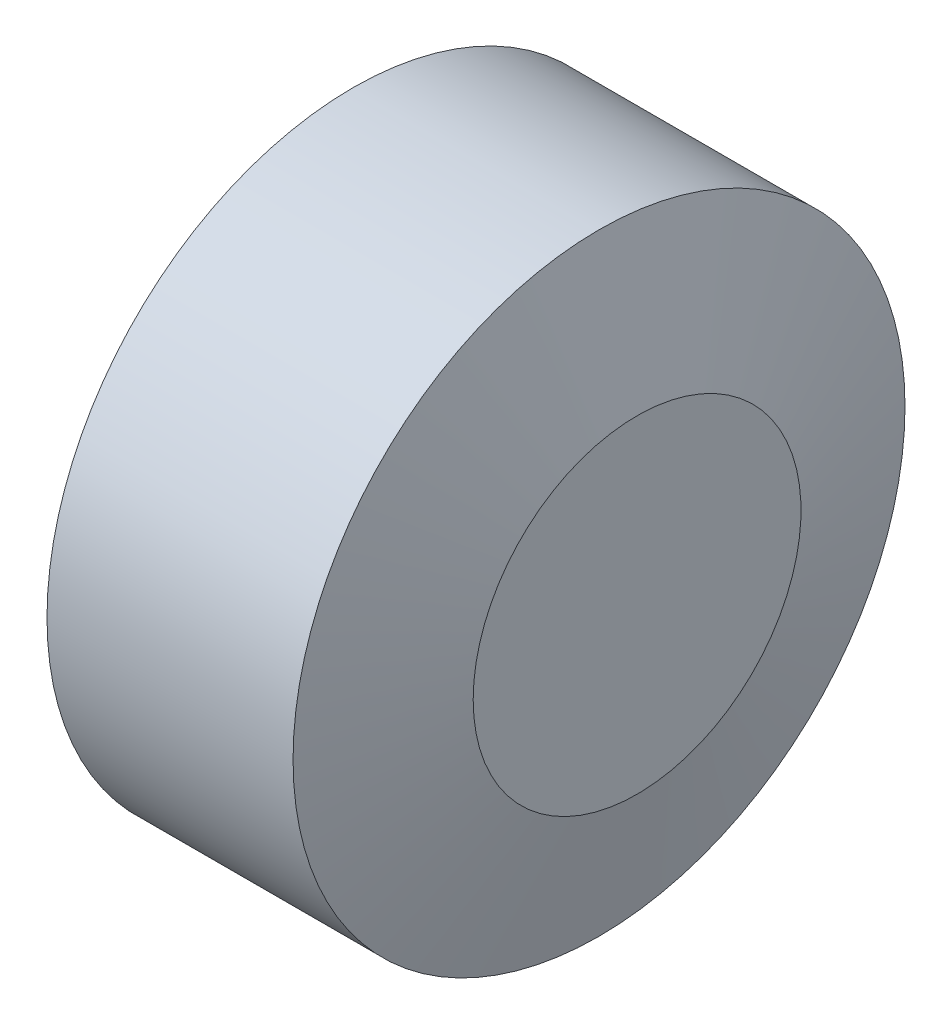
SolidWorks part; units mm, degrees
ref_plane "Ebene vorne" through (0, 0, 0) normal (0, 0, 1) x (1, 0, 0)
ref_plane "Ebene oben" through (0, 0, 0) normal (0, 1, 0) x (1, 0, 0)
ref_plane "Ebene rechts" through (0, 0, 0) normal (1, 0, 0) x (0, 0, -1)
sketch "Skizze1" plane through (0, 0, 0) normal (0, 0, 1) x (1, 0, 0)
  line L0 (0, 0) -> (56.0834, 0) construction
  line L1 (0, 0) -> (0, -14)
  line L2 (0, -14) -> (11.2583, -14)
  line L3 (11.2583, -14) -> (13, -7.5)
  line L4 (13, -7.5) -> (13, 0)
  line L5 (0, 0) -> (13, 0)
  dimension "D1" = 28
  dimension "D2" = 15
  dimension "D3" = 13
  dimension "D4" = 15
revolve "Rotation1" add sketch "Skizze1" angle 360 about L0
sketch "Skizze13" plane through (13, 0, 0) normal (1, 0, 0) x (0, 0, -1)
  line L0 (11.2845, 1.5799) -> (11.3741, 0.6083)
  line L1 (11.3741, 0.6083) -> (11.2845, 1.5799)
  line L2 (12.3428, 1.2588) -> (9.452, 0.9909)
  line L4 (9.5613, 3.6387) -> (9.5927, 2.9574)
  line L5 (8.5478, 3.7436) -> (8.6967, 3.8751)
  line L7 (8.7106, 5.0765) -> (7.4768, 6.7494)
  line L9 (6.869, 10.1322) -> (4.9357, 7.2875)
  line L10 (4.9357, 7.2875) -> (6.869, 10.1322)
  line L11 (5.8093, 10.8519) -> (7.9286, 9.4117)
  line L12 (7.9286, 9.4117) -> (5.8093, 10.8519)
  circle A1 centre (0, 0) radius 8.9821 construction
  spline S0 degree 3 poles (9.452, 0.9909) (9.4078, 0.9865) (9.3416, 0.9742) (9.2592, 0.9408) (9.2001, 0.9101) (9.1449, 0.8728) (9.0789, 0.8122) (9.0356, 0.7605) (9.0135, 0.7209) knots 0 0 0 0 0.250138 0.374097 0.498215 0.623467 0.746733 1 1 1 1
  spline S1 degree 3 poles (9.0135, 0.7209) (8.9889, 0.684) (8.961, 0.6237) (8.9352, 0.539) (8.9234, 0.4736) (8.9192, 0.4069) (8.9238, 0.3172) (8.9394, 0.2511) (8.954, 0.2083) knots 0 0 0 0 0.248261 0.371336 0.496457 0.621138 0.745744 1 1 1 1
  spline S2 degree 3 poles (10.5482, 2.721) (10.6028, 2.7556) (10.7013, 2.8473) (10.759, 2.9687) (10.779, 3.0329) knots 0 0 0 0 0.489493 1 1 1 1
  spline S3 degree 3 poles (10.779, 3.0329) (10.7979, 3.0978) (10.8228, 3.2352) (10.8159, 3.3745) (10.807, 3.4449) knots 0 0 0 0 0.487714 1 1 1 1
  spline S4 degree 3 poles (10.807, 3.4449) (10.7969, 3.5156) (10.762, 3.6557) (10.7041, 3.7878) (10.6692, 3.8513) knots 0 0 0 0 0.49623 1 1 1 1
  spline S5 degree 3 poles (10.6692, 3.8513) (10.6339, 3.9127) (10.5568, 4.0246) (10.4571, 4.117) (10.4041, 4.1534) knots 0 0 0 0 0.52472 1 1 1 1
  spline S6 degree 3 poles (10.4041, 4.1534) (10.3566, 4.1885) (10.2561, 4.2492) (10.1407, 4.2733) (10.0837, 4.2731) knots 0 0 0 0 0.510177 1 1 1 1
  spline S7 degree 3 poles (10.0837, 4.2731) (10.0271, 4.2755) (9.9056, 4.2516) (9.8009, 4.1862) (9.7501, 4.1458) knots 0 0 0 0 0.464078 1 1 1 1
  spline S8 degree 3 poles (9.7501, 4.1458) (9.7231, 4.1204) (9.6846, 4.077) (9.6474, 4.0071) (9.621, 3.9472) (9.5997, 3.8798) (9.5757, 3.7769) (9.5655, 3.6952) (9.5613, 3.6387) knots 0 0 0 0 0.201067 0.31074 0.427827 0.555243 0.692797 1 1 1 1
  spline S9 degree 3 poles (9.5927, 2.9574) (9.5964, 2.8899) (9.5966, 2.7631) (9.5665, 2.6398) (9.5459, 2.5853) knots 0 0 0 0 0.537618 1 1 1 1
  spline S10 degree 3 poles (9.5459, 2.5853) (9.5271, 2.5357) (9.4771, 2.4431) (9.4066, 2.365) (9.3675, 2.3314) knots 0 0 0 0 0.507486 1 1 1 1
  spline S11 degree 3 poles (9.3675, 2.3314) (9.3271, 2.2998) (9.2348, 2.2488) (9.13, 2.2362) (9.0779, 2.2384) knots 0 0 0 0 0.495838 1 1 1 1
  spline S12 degree 3 poles (9.0779, 2.2384) (9.022, 2.2405) (8.9062, 2.2649) (8.8027, 2.3221) (8.7527, 2.3573) knots 0 0 0 0 0.477202 1 1 1 1
  spline S13 degree 3 poles (8.7527, 2.3573) (8.6992, 2.3921) (8.6, 2.4853) (8.5226, 2.597) (8.4876, 2.6594) knots 0 0 0 0 0.470377 1 1 1 1
  spline S14 degree 3 poles (8.4876, 2.6594) (8.4508, 2.7209) (8.3921, 2.8532) (8.3592, 2.994) (8.3498, 3.0658) knots 0 0 0 0 0.497265 1 1 1 1
  spline S15 degree 3 poles (8.3498, 3.0658) (8.3394, 3.1345) (8.3344, 3.2712) (8.3595, 3.4057) (8.3813, 3.4687) knots 0 0 0 0 0.510753 1 1 1 1
  spline S16 degree 3 poles (8.3813, 3.4687) (8.3981, 3.5244) (8.4412, 3.6249) (8.5085, 3.7115) (8.5478, 3.7436) knots 0 0 0 0 0.536048 1 1 1 1
  spline S17 degree 3 poles (8.0098, 4.8366) (7.9364, 4.8344) (7.7891, 4.8419) (7.6461, 4.8784) (7.5768, 4.9023) knots 0 0 0 0 0.500142 1 1 1 1
  spline S18 degree 3 poles (7.5768, 4.9023) (7.5316, 4.9195) (7.4648, 4.947) (7.3821, 4.9952) (7.3241, 5.0352) (7.2688, 5.0785) (7.2182, 5.1273) (7.1693, 5.1789) (7.1251, 5.2354) (7.0847, 5.2946) (7.0484, 5.3557) (7.0187, 5.4194) (6.9936, 5.4847) (6.9721, 5.5513) (6.9514, 5.6439) (6.9451, 5.7154) (6.9424, 5.7633) knots 0 0 0 0 0.127666 0.190265 0.252235 0.31356 0.375383 0.437654 0.501191 0.564524 0.626591 0.688537 0.749914 0.811229 0.873046 1 1 1 1
  spline S19 degree 3 poles (6.9424, 5.7633) (6.9408, 5.866) (6.9568, 6.0199) (7.0151, 6.2171) (7.0777, 6.3586) (7.1555, 6.4926) (7.2798, 6.6571) (7.3933, 6.7627) (7.4761, 6.8237) knots 0 0 0 0 0.249815 0.373527 0.49931 0.625449 0.749841 1 1 1 1
  spline S20 degree 3 poles (7.4761, 6.8237) (7.5584, 6.8856) (7.6933, 6.9619) (7.8871, 7.0318) (8.0379, 7.0664) (8.1916, 7.0843) (8.3976, 7.0824) (8.5498, 7.0522) (8.6476, 7.0202) knots 0 0 0 0 0.250179 0.374318 0.500057 0.625629 0.749837 1 1 1 1
  spline S21 degree 3 poles (8.6476, 7.0202) (8.693, 7.0042) (8.7589, 6.976) (8.841, 6.9286) (8.8992, 6.8898) (8.9532, 6.8455) (9.0054, 6.7986) (9.0525, 6.7455) (9.0976, 6.6899) (9.1379, 6.6306) (9.1734, 6.5691) (9.2047, 6.506) (9.2296, 6.4402) (9.251, 6.3729) (9.271, 6.2792) (9.2809, 6.2077) (9.282, 6.1592) knots 0 0 0 0 0.12689 0.188652 0.250278 0.311125 0.372982 0.435293 0.498351 0.561688 0.62429 0.685951 0.747331 0.809824 0.872245 1 1 1 1
  spline S22 degree 3 poles (9.282, 6.1592) (9.2836, 6.0531) (9.2682, 5.8934) (9.206, 5.6896) (9.1401, 5.5436) (9.0572, 5.4067) (8.924, 5.239) (8.8001, 5.1354) (8.7106, 5.0765) knots 0 0 0 0 0.249225 0.373386 0.498834 0.624353 0.74823 1 1 1 1
sketch "Skizze14" plane through (13, 0, 0) normal (1, 0, 0) x (0, 0, -1)
  line L1 (8.7106, 5.0765) -> (7.4768, 6.7494) construction
  line L2 (8.7106, 5.0765) -> (7.4768, 6.7494)
  spline S0 degree 3 poles (-1504.7271, -1303.0515) (34.3407, 79.4947) (-4.2637, -73.8144) (4.661, 87.6769) (1231.772, -1576.2357) knots -50.963163 -50.963163 -50.963163 -50.963163 0.500142 53.15614 53.15614 53.15614 53.15614 only from (8.0098, 4.8366) to (7.5768, 4.9023) construction
  spline S1 degree 3 poles (-1103.2655, -1658.161) (30.3504, 31.0888) (11.0666, 2.8493) (7.3821, 4.9952) (7.3241, 5.0352) (7.2688, 5.0785) (7.2182, 5.1273) (7.1693, 5.1789) (7.1251, 5.2354) (7.0847, 5.2946) (7.0484, 5.3557) (7.0187, 5.4194) (6.9936, 5.4847) (6.9721, 5.5513) (5.9893, 9.9536) (41.2588, 20.4289) (-1904.0188, -583.9593) knots -10.987318 -10.987318 -10.987318 -10.987318 0.127666 0.190265 0.252235 0.31356 0.375383 0.437654 0.501191 0.564524 0.626591 0.688537 0.749914 0.811229 0.873046 12.638524 12.638524 12.638524 12.638524 only from (7.5768, 4.9023) to (6.9424, 5.7633) construction
  spline S2 degree 3 poles (290.3759, 1984.1174) (99.2879, -33.5022) (4.4077, -2.6079) (7.0151, 6.2171) (7.0777, 6.3586) (7.1555, 6.4926) (12.8733, 14.0641) (95.4639, -44.1594) (-1427.223, -1384.4174) knots -21.837368 -21.837368 -21.837368 -21.837368 0.249815 0.373527 0.49931 0.625449 0.749841 23.536745 23.536745 23.536745 23.536745 only from (6.9424, 5.7633) to (7.4761, 6.8237) construction
  spline S3 degree 3 poles (1982.0417, -304.7734) (23.8517, -74.9215) (-0.3269, 4.0696) (7.8871, 7.0318) (8.0379, 7.0664) (8.1916, 7.0843) (17.28, 7.0015) (19.0596, -91.9283) (-1935.5645, 470.107) knots -20.692282 -20.692282 -20.692282 -20.692282 0.250179 0.374318 0.500057 0.625629 0.749837 22.549034 22.549034 22.549034 22.549034 only from (7.4761, 6.8237) to (8.6476, 7.0202) construction
  spline S4 degree 3 poles (1813.2868, 868.7619) (-33.1273, -45.2984) (3.3889, 10.0808) (8.841, 6.9286) (8.8992, 6.8898) (8.9532, 6.8455) (9.0054, 6.7986) (9.0525, 6.7455) (9.0976, 6.6899) (9.1379, 6.6306) (9.1734, 6.5691) (9.2047, 6.506) (9.2296, 6.4402) (9.251, 6.3729) (10.1299, 2.2648) (-6.5263, -5.0538) (-1990.0024, -42.644) knots -16.36419 -16.36419 -16.36419 -16.36419 0.12689 0.188652 0.250278 0.311125 0.372982 0.435293 0.498351 0.561688 0.62429 0.685951 0.747331 0.809824 0.872245 11.827501 11.827501 11.827501 11.827501 only from (8.6476, 7.0202) to (9.282, 6.1592) construction
  spline S5 degree 3 poles (858.7258, -1803.8846) (-75.3502, 42.7074) (11.7151, 13.9046) (9.206, 5.6896) (9.1401, 5.5436) (9.0572, 5.4067) (3.6749, -1.3688) (-70.8363, 55.1198) (1947.1145, 494.5404) knots -19.608757 -19.608757 -19.608757 -19.608757 0.249225 0.373386 0.498834 0.624353 0.74823 20.755578 20.755578 20.755578 20.755578 only from (9.282, 6.1592) to (8.7106, 5.0765) construction
  spline S6 degree 3 poles (8.0098, 4.8366) (7.9364, 4.8344) (7.7891, 4.8419) (7.6461, 4.8784) (7.5768, 4.9023) knots 0 0 0 0 0.500142 1 1 1 1
  spline S7 degree 3 poles (7.5768, 4.9023) (7.5316, 4.9195) (7.4648, 4.947) (7.3821, 4.9952) (7.3241, 5.0352) (7.2688, 5.0785) (7.2182, 5.1273) (7.1693, 5.1789) (7.1251, 5.2354) (7.0847, 5.2946) (7.0484, 5.3557) (7.0187, 5.4194) (6.9936, 5.4847) (6.9721, 5.5513) (6.9514, 5.6439) (6.9451, 5.7154) (6.9424, 5.7633) knots 0 0 0 0 0.127666 0.190265 0.252235 0.31356 0.375383 0.437654 0.501191 0.564524 0.626591 0.688537 0.749914 0.811229 0.873046 1 1 1 1
  spline S8 degree 3 poles (6.9424, 5.7633) (6.9408, 5.866) (6.9568, 6.0199) (7.0151, 6.2171) (7.0777, 6.3586) (7.1555, 6.4926) (7.2798, 6.6571) (7.3933, 6.7627) (7.4761, 6.8237) knots 0 0 0 0 0.249815 0.373527 0.49931 0.625449 0.749841 1 1 1 1
  spline S9 degree 3 poles (7.4761, 6.8237) (7.5584, 6.8856) (7.6933, 6.9619) (7.8871, 7.0318) (8.0379, 7.0664) (8.1916, 7.0843) (8.3976, 7.0824) (8.5498, 7.0522) (8.6476, 7.0202) knots 0 0 0 0 0.250179 0.374318 0.500057 0.625629 0.749837 1 1 1 1
  spline S10 degree 3 poles (8.6476, 7.0202) (8.693, 7.0042) (8.7589, 6.976) (8.841, 6.9286) (8.8992, 6.8898) (8.9532, 6.8455) (9.0054, 6.7986) (9.0525, 6.7455) (9.0976, 6.6899) (9.1379, 6.6306) (9.1734, 6.5691) (9.2047, 6.506) (9.2296, 6.4402) (9.251, 6.3729) (9.271, 6.2792) (9.2809, 6.2077) (9.282, 6.1592) knots 0 0 0 0 0.12689 0.188652 0.250278 0.311125 0.372982 0.435293 0.498351 0.561688 0.62429 0.685951 0.747331 0.809824 0.872245 1 1 1 1
  spline S11 degree 3 poles (9.282, 6.1592) (9.2836, 6.0531) (9.2682, 5.8934) (9.206, 5.6896) (9.1401, 5.5436) (9.0572, 5.4067) (8.924, 5.239) (8.8001, 5.1354) (8.7106, 5.0765) knots 0 0 0 0 0.249225 0.373386 0.498834 0.624353 0.74823 1 1 1 1
surface "Oberfläche-Linear austragen1" sketch "Skizze14" parameters "D1"=2
sketch3d "3D-Skizze1"
  spline S0 degree 3 poles (563.4894, 126.8058, 1909.0127) (-569.3116, 84.2805, -1935.9737) (616.1384, -271.3031, 1894.5644) (-604.1889, 473.0336, -1849.8554) knots -62.159292 -62.159292 -62.159292 -62.159292 61.590799 61.590799 61.590799 61.590799 only from (12.5025, 4.8366, -8.0098) to (12.5915, 4.9023, -7.5768)
  spline S1 degree 3 poles (474.6148, -1730.0515, 873.5191) (3.1771, 30.5352, -30.0528) (12.0661, 3.0236, -11.1848) (12.6184, 4.9804, -7.4053) (12.6234, 5.0058, -7.3655) (12.6361, 5.0902, -7.2501) (12.6403, 5.1582, -7.1826) (12.6403, 5.2732, -7.0984) (12.6394, 5.3137, -7.072) (12.6353, 5.3975, -7.0276) (12.632, 5.441, -7.0097) (12.6239, 5.5298, -6.9783) (12.6189, 5.5757, -6.9656) (12.0355, 10.0017, -6.1884) (2.863, 17.4836, -40.969) (455.9303, -154.1766, 1936.6955) knots -11.056555 -11.056555 -11.056555 -11.056555 0.125 0.125 0.25 0.25 0.5 0.5 0.625 0.625 0.75 0.75 0.875 0.875 12.596374 12.596374 12.596374 12.596374 only from (12.5915, 4.9023, -7.5768) to (12.5919, 5.7633, -6.9424)
  spline S2 degree 3 poles (-608.0045, 1567.3574, -1088.4183) (7.7561, -57.6744, -86.6707) (14.7545, -1.7955, -2.8924) (12.4332, 6.4522, -7.129) (12.4063, 6.5385, -7.1865) (9.7059, 14.2616, -13.7827) (2.4061, -50.3754, -109.5726) (517.8097, -1599.3003, 1067.7779) knots -21.916046 -21.916046 -21.916046 -21.916046 0.5 0.5 0.75 0.75 25.513217 25.513217 25.513217 25.513217 only from (12.5919, 5.7633, -6.9424) to (12.2974, 6.8237, -7.4761)
  spline S3 degree 3 poles (-316.3948, -25.8526, -1978.4671) (28.7971, -90.4228, -6.9903) (14.2742, 5.4609, 1.1461) (12.1196, 7.0807, -8.1364) (12.0972, 7.087, -8.2413) (9.1261, 6.0048, -23.7019) (56.4502, -277.1411, -11.8593) (-99.6589, -1975.7887, 219.9496) knots -22.25953 -22.25953 -22.25953 -22.25953 0.5 0.5 0.75 0.75 38.201148 38.201148 38.201148 38.201148 only from (12.2974, 6.8237, -7.4761) to (12.0251, 7.0202, -8.6476)
  spline S4 degree 3 poles (-401.1474, 1761.1895, -875.7041) (40.4205, -91.641, 59.7712) (12.6094, 11.8616, -2.144) (11.9874, 6.8336, -8.9737) (11.9842, 6.7653, -9.0404) (11.984, 6.6125, -9.1538) (11.9874, 6.5277, -9.1987) (12.4483, 0.5671, -11.2592) (26.0076, -27.1868, 37.1233) (221.4731, 1156.4556, 1612.7202) knots -21.796836 -21.796836 -21.796836 -21.796836 0.25 0.25 0.5 0.5 0.75 0.75 17.167221 17.167221 17.167221 17.167221 only from (12.0251, 7.0202, -8.6476) to (12.0248, 6.1592, -9.282)
  spline S5 degree 3 poles (-556.8961, -344.3255, -1894.1163) (37.8795, 58.2084, 148.214) (9.8748, 17.0428, -11.903) (12.0994, 5.7353, -9.2236) (12.1226, 5.6338, -9.1844) (12.1714, 5.4466, -9.0849) (12.1977, 5.3581, -9.0233) (15.1741, -3.1918, -1.1699) (26.3816, 111.7393, 116.7) (-21.6415, -1499.6789, -1325.5134) knots -26.644147 -26.644147 -26.644147 -26.644147 0.25 0.25 0.5 0.5 0.75 0.75 27.950023 27.950023 27.950023 27.950023 only from (12.0248, 6.1592, -9.282) to (12.3082, 5.0765, -8.7106)
  spline S6 degree 3 poles (-1935.9348, -337.6562, -261.4777) (131.8698, -129.2041, -107.7432) (1148.3326, 80.2652, 46.7415) (-1949.4445, 293.7152, 204.1619) knots -205.993222 -205.993222 -205.993222 -205.993222 171.397562 171.397562 171.397562 171.397562 only from (12.3082, 5.0765, -8.7106) to (12.3107, 6.7494, -7.4768)
  spline S7 degree 3 poles (12.3082, 5.0765, -8.7106) (12.3281, 5.6341, -8.2993) (12.329, 6.1918, -7.8881) (12.3107, 6.7494, -7.4768) knots 0 0 0 0 1 1 1 1
  spline S8 degree 3 poles (12.0248, 6.1592, -9.282) (12.0405, 6.0503, -9.2836) (12.0584, 5.9435, -9.273) (12.0994, 5.7353, -9.2236) (12.1226, 5.6338, -9.1844) (12.1714, 5.4466, -9.0849) (12.1977, 5.3581, -9.0233) (12.2519, 5.2024, -8.8803) (12.2797, 5.1349, -8.7994) (12.3082, 5.0765, -8.7106) knots 0 0 0 0 0.25 0.25 0.5 0.5 0.75 0.75 1 1 1 1
  spline S9 degree 3 poles (12.0251, 7.0202, -8.6476) (12.0118, 6.9887, -8.7369) (12.0014, 6.9463, -8.8205) (11.9874, 6.8336, -8.9737) (11.9842, 6.7653, -9.0404) (11.984, 6.6125, -9.1538) (11.9874, 6.5277, -9.1987) (12.0012, 6.3489, -9.2605) (12.0112, 6.2544, -9.2797) (12.0248, 6.1592, -9.282) knots 0 0 0 0 0.25 0.25 0.5 0.5 0.75 0.75 1 1 1 1
  spline S10 degree 3 poles (12.2974, 6.8237, -7.4761) (12.2426, 6.9472, -7.6404) (12.1898, 7.0279, -7.8338) (12.1196, 7.0807, -8.1364) (12.0972, 7.087, -8.2413) (12.0578, 7.0726, -8.4463) (12.0404, 7.0529, -8.5476) (12.0251, 7.0202, -8.6476) knots 0 0 0 0 0.5 0.5 0.75 0.75 1 1 1 1
  spline S11 degree 3 poles (12.5919, 5.7633, -6.9424) (12.5566, 5.9736, -6.9391) (12.51, 6.1793, -6.9888) (12.4332, 6.4522, -7.129) (12.4063, 6.5385, -7.1865) (12.3523, 6.6929, -7.3183) (12.3248, 6.7627, -7.3934) (12.2974, 6.8237, -7.4761) knots 0 0 0 0 0.5 0.5 0.75 0.75 1 1 1 1
  spline S12 degree 3 poles (12.5915, 4.9023, -7.5768) (12.599, 4.9191, -7.5325) (12.6062, 4.9371, -7.4889) (12.6184, 4.9804, -7.4053) (12.6234, 5.0058, -7.3655) (12.6361, 5.0902, -7.2501) (12.6403, 5.1582, -7.1826) (12.6403, 5.2732, -7.0984) (12.6394, 5.3137, -7.072) (12.6353, 5.3975, -7.0276) (12.632, 5.441, -7.0097) (12.6239, 5.5298, -6.9783) (12.6189, 5.5757, -6.9656) (12.6066, 5.6691, -6.9492) (12.5995, 5.7161, -6.945) (12.5919, 5.7633, -6.9424) knots 0 0 0 0 0.125 0.125 0.25 0.25 0.5 0.5 0.625 0.625 0.75 0.75 0.875 0.875 1 1 1 1
  spline S13 degree 3 poles (12.5025, 4.8366, -8.0098) (12.5366, 4.8323, -7.8638) (12.5671, 4.854, -7.7168) (12.5915, 4.9023, -7.5768) knots 0 0 0 0 1 1 1 1
